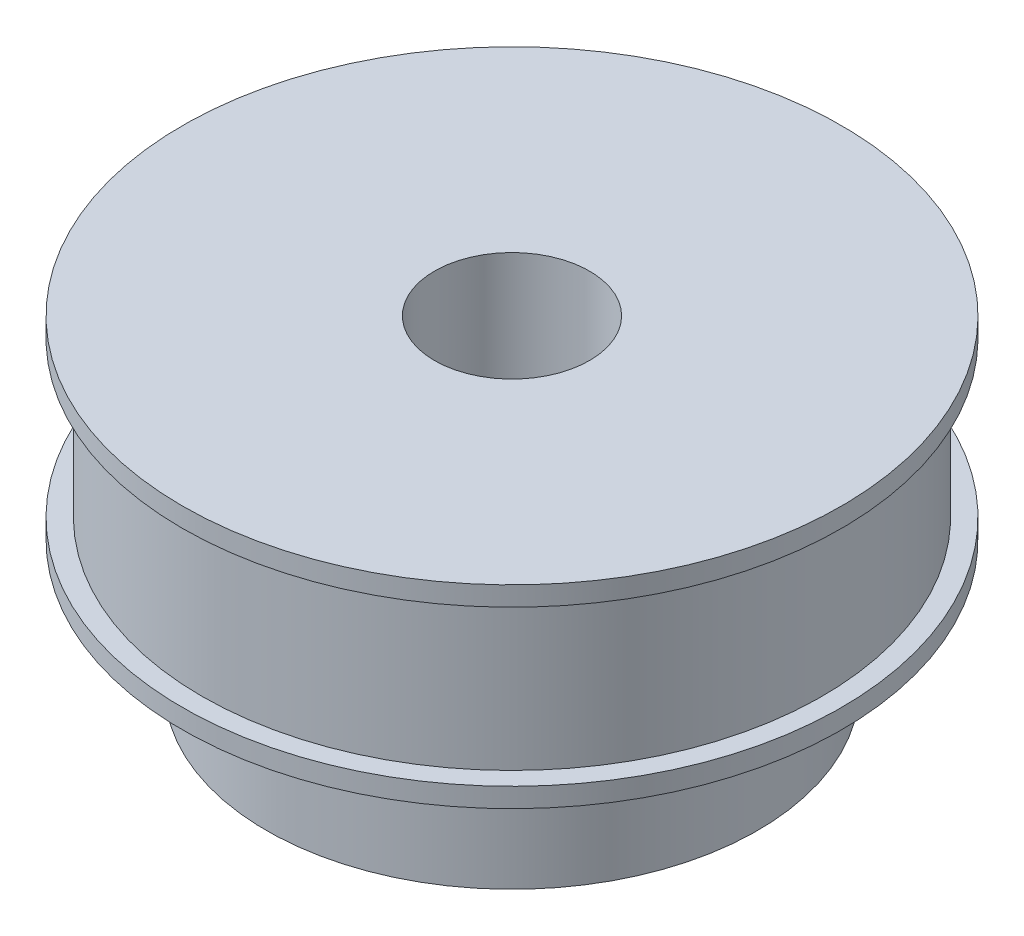
SolidWorks part; units mm, degrees
material "4032-T6"
ref_plane "Front Plane" through (0, 0, 0) normal (0, 0, 1) x (1, 0, 0)
ref_plane "Top Plane" through (0, 0, 0) normal (0, 1, 0) x (1, 0, 0)
ref_plane "Right Plane" through (0, 0, 0) normal (1, 0, 0) x (0, 0, -1)
sketch "Sketch1" plane through (0, 0, 0) normal (0, 1, 0) x (1, 0, 0)
  circle A0 centre (0, 0) radius 24
  dimension "D1" = 48
extrude "Boss-Extrude1" add sketch "Sketch1" along normal blind 12
sketch "Sketch3" plane through (0, 12, 0) normal (0, 1, 0) x (1, 0, 0)
  circle A0 centre (0, 0) radius 25.5
  dimension "D1" = 51
extrude "Boss-Extrude3" add sketch "Sketch3" along normal blind 1.5
sketch "Sketch4" plane through (0, 0, 0) normal (0, -1, 0) x (1, 0, 0)
  circle A0 centre (0, 0) radius 25.5
  dimension "D1" = 51
extrude "Boss-Extrude4" add sketch "Sketch4" along normal blind 1.5
sketch "Sketch5" plane through (0, -1.5, 0) normal (0, -1, 0) x (1, 0, 0)
  circle A0 centre (0, 0) radius 19
  dimension "D1" = 38
extrude "Boss-Extrude5" add sketch "Sketch5" along normal blind 10
sketch "Sketch6" plane through (0, 13.5, 0) normal (0, 1, 0) x (1, 0, 0)
  circle A0 centre (0, 0) radius 6
  dimension "D1" = 12
extrude "Cut-Extrude1" cut sketch "Sketch6" against normal up to surface (25 mm away) up to face at (0, -11.5, -19)
